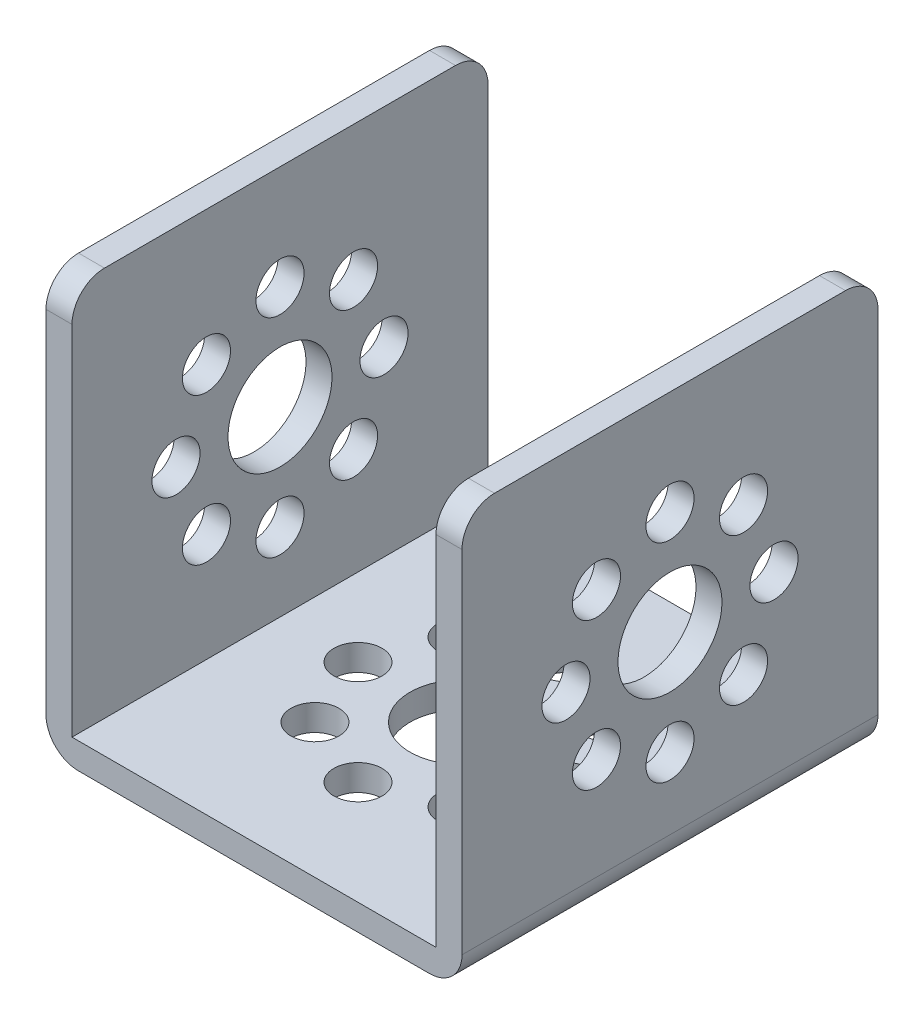
SolidWorks part; units mm, degrees
material "2024 Alloy"
ref_plane "Front Plane" through (0, 0, 0) normal (0, 0, 1) x (1, 0, 0)
ref_plane "Top Plane" through (0, 0, 0) normal (0, 1, 0) x (1, 0, 0)
ref_plane "Right Plane" through (0, 0, 0) normal (1, 0, 0) x (0, 0, -1)
ref_plane "Plane1" through (16, 0, 0) normal (1, 0, 0) x (0, 0, -1)
sketch "Sketch1" plane through (16, 0, 0) normal (1, 0, 0) x (0, 0, -1)
  line L0 (-16, 32) -> (-16, 0)
  line L1 (-16, 0) -> (16, 0)
  line L2 (16, 0) -> (16, 32)
  line L3 (16, 32) -> (-16, 32)
extrude "Boss-Extrude1" add sketch "Sketch1" against normal blind 32
sketch "Sketch2" plane through (0, 0, -16) normal (0, 0, -1) x (-1, 0, 0)
  line L0 (14, 32) -> (-14, 32)
  line L1 (-14, 32) -> (-14, 2)
  line L2 (-14, 2) -> (14, 2)
  line L3 (14, 2) -> (14, 32)
extrude "Cut-Extrude1" cut sketch "Sketch2" against normal through all
hole_wizard "Ø8.0 (8) Diameter Hole1" positions "Sketch4" profile "Sketch3" hole size "Ø8.0" standard "ANSI Metric"
sketch "Sketch4" plane through (-16, 0, 0) normal (-1, 0, 0) x (0, 0, 1)
  point P0 (0, 16)
sketch "Sketch3" plane through (-16, 16, 0) normal (0, 1, 0) x (0, 0, 1)
  line L0 (0, 0) -> (0, 2)
  line L1 (0, 2) -> (4, 2)
  line L2 (4, 2) -> (4, 0)
  line L5 (4, 0) -> (0, 0)
  line L11 (0, -6.35) -> (0, 107.95) construction
  dimension "Thru Hole Dia." = 8
  dimension "Thru Hole Depth" = 2
hole_wizard "Ø3.7 (3.7) Diameter Hole1" positions "Sketch6" profile "Sketch5" hole size "Ø3.7" standard "ANSI Metric"
sketch "Sketch6" plane through (-16, 0, 0) normal (-1, 0, 0) x (0, 0, 1)
  point P0 (-8, 16)
  point P1 (0, 24)
  point P2 (8, 16)
  point P3 (0, 8)
  point P4 (-5.6569, 21.6569)
  point P5 (5.6569, 21.6569)
  point P6 (5.6569, 10.3431)
  point P7 (-5.6569, 10.3431)
sketch "Sketch5" plane through (-16, 16, -8) normal (0, 1, 0) x (0, 0, 1)
  line L0 (0, 0) -> (0, 2)
  line L1 (0, 2) -> (1.85, 2)
  line L2 (1.85, 2) -> (1.85, 0)
  line L5 (1.85, 0) -> (0, 0)
  line L11 (0, -6.35) -> (0, 107.95) construction
  dimension "Thru Hole Dia." = 3.7
  dimension "Thru Hole Depth" = 2
hole_wizard "Ø3.7 (3.7) Diameter Hole2" positions "Sketch8" profile "Sketch7" hole size "Ø3.7" standard "ANSI Metric"
sketch "Sketch8" plane through (0, 2, 0) normal (0, 1, 0) x (1, 0, 0)
  point P0 (8, 0)
  point P1 (0, 8)
  point P2 (-8, 0)
  point P3 (0, -8)
  point P4 (5.6569, 5.6569)
  point P5 (-5.6569, 5.6569)
  point P6 (-5.6569, -5.6569)
  point P7 (5.6569, -5.6569)
sketch "Sketch7" plane through (8, 2, 0) normal (1, 0, 0) x (0, 0, 1)
  line L0 (0, 0) -> (0, 2)
  line L1 (0, 2) -> (1.85, 2)
  line L2 (1.85, 2) -> (1.85, 0)
  line L5 (1.85, 0) -> (0, 0)
  line L11 (0, -6.35) -> (0, 107.95) construction
  dimension "Thru Hole Dia." = 3.7
  dimension "Thru Hole Depth" = 2
hole_wizard "Ø8.0 (8) Diameter Hole2" positions "Sketch10" profile "Sketch9" hole size "Ø8.0" standard "ANSI Metric"
sketch "Sketch10" plane through (0, 0, 0) normal (0, -1, 0) x (-1, 0, 0)
  point P0 (0, 0)
sketch "Sketch9" plane through (0, 0, 0) normal (1, 0, 0) x (0, 0, -1)
  line L0 (0, 0) -> (0, 32)
  line L1 (0, 32) -> (4, 32)
  line L2 (4, 32) -> (4, 0)
  line L5 (4, 0) -> (0, 0)
  line L11 (0, -6.35) -> (0, 107.95) construction
  dimension "Thru Hole Dia." = 8
  dimension "Thru Hole Depth" = 32
hole_wizard "Ø8.0 (8) Diameter Hole3" positions "Sketch12" profile "Sketch11" hole size "Ø8.0" standard "ANSI Metric"
sketch "Sketch12" plane through (16, 0, 0) normal (1, 0, 0) x (0, 0, -1)
  point P0 (0, 16)
sketch "Sketch11" plane through (16, 16, 0) normal (0, 1, 0) x (0, 0, -1)
  line L0 (0, 0) -> (0, 32)
  line L1 (0, 32) -> (4, 32)
  line L2 (4, 32) -> (4, 0)
  line L5 (4, 0) -> (0, 0)
  line L11 (0, -6.35) -> (0, 107.95) construction
  dimension "Thru Hole Dia." = 8
  dimension "Thru Hole Depth" = 32
hole_wizard "Ø3.7 (3.7) Diameter Hole3" positions "Sketch14" profile "Sketch13" hole size "Ø3.7" standard "ANSI Metric"
sketch "Sketch14" plane through (16, 0, 0) normal (1, 0, 0) x (0, 0, -1)
  point P0 (8, 16)
  point P1 (0, 24)
  point P2 (-8, 16)
  point P3 (0, 8)
  point P4 (5.6569, 21.6569)
  point P5 (-5.6569, 21.6569)
  point P6 (-5.6569, 10.3431)
  point P7 (5.6569, 10.3431)
sketch "Sketch13" plane through (16, 16, -8) normal (0, 1, 0) x (0, 0, -1)
  line L0 (0, 0) -> (0, 32)
  line L1 (0, 32) -> (1.85, 32)
  line L2 (1.85, 32) -> (1.85, 0)
  line L5 (1.85, 0) -> (0, 0)
  line L11 (0, -6.35) -> (0, 107.95) construction
  dimension "Thru Hole Dia." = 3.7
  dimension "Thru Hole Depth" = 32
fillet "Fillet1" radius 2.5 6 edges at (-16, 0, 0) (-15, 32, 16) (-15, 32, -16) (16, 0, 0) (15, 32, 16) (15, 32, -16)
